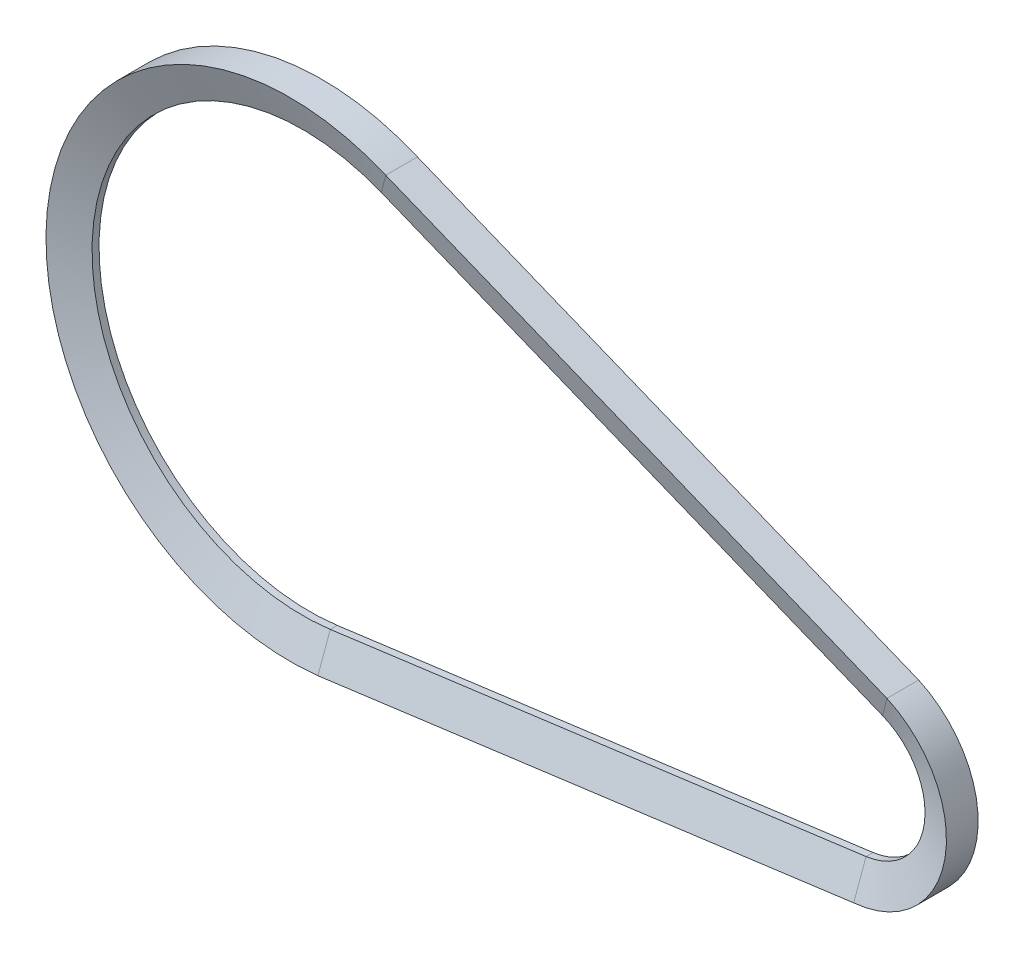
SolidWorks part; units mm, degrees
ref_plane "Front Plane" through (0, 0, 0) normal (0, 0, 1) x (1, 0, 0)
ref_plane "Top Plane" through (0, 0, 0) normal (0, 1, 0) x (1, 0, 0)
ref_plane "Right Plane" through (0, 0, 0) normal (1, 0, 0) x (0, 0, -1)
sketch "Sketch1" plane through (0, 0, 0) normal (0, 0, 1) x (1, 0, 0)
  line L0 (6.1247, -46.0949) -> (124.4757, -30.3693)
  line L1 (17.4127, 43.1167) -> (128.117, -1.5914)
  arc A0 (17.4127, 43.1167) -> (6.1247, -46.0949) centre (0, 0) ccw
  arc A1 (124.4757, -30.3693) -> (128.117, -1.5914) centre (122.5, -15.5) ccw
  dimension "D3" = 93
  dimension "D4" = 30
  dimension "D1" = 15.5
  dimension "D2" = 122.5
ref_plane "Plane1" through (6.1247, 0, 0) normal (1, 0, 0) x (0, 0, -1)
sketch "Sketch2" plane through (6.1247, 0, 0) normal (1, 0, 0) x (0, 0, -1)
  line L0 (0, -46.0949) -> (0, -12.8248) construction
  line L1 (-0.7702, -46.0949) -> (0.7702, -46.0949)
  line L2 (-3.5, -53.5949) -> (3.5, -53.5949)
  line L3 (3.5, -53.5949) -> (0.7702, -46.0949)
  line L4 (-0.7702, -46.0949) -> (-3.5, -53.5949)
  line L5 (0, -46.0949) -> (0, -53.5949) construction
  dimension "D1" = 7
  dimension "D2" = 7.5
  dimension "D3" = 40
sweep "Sweep1" add profiles "Sketch2" path "Sketch1"
